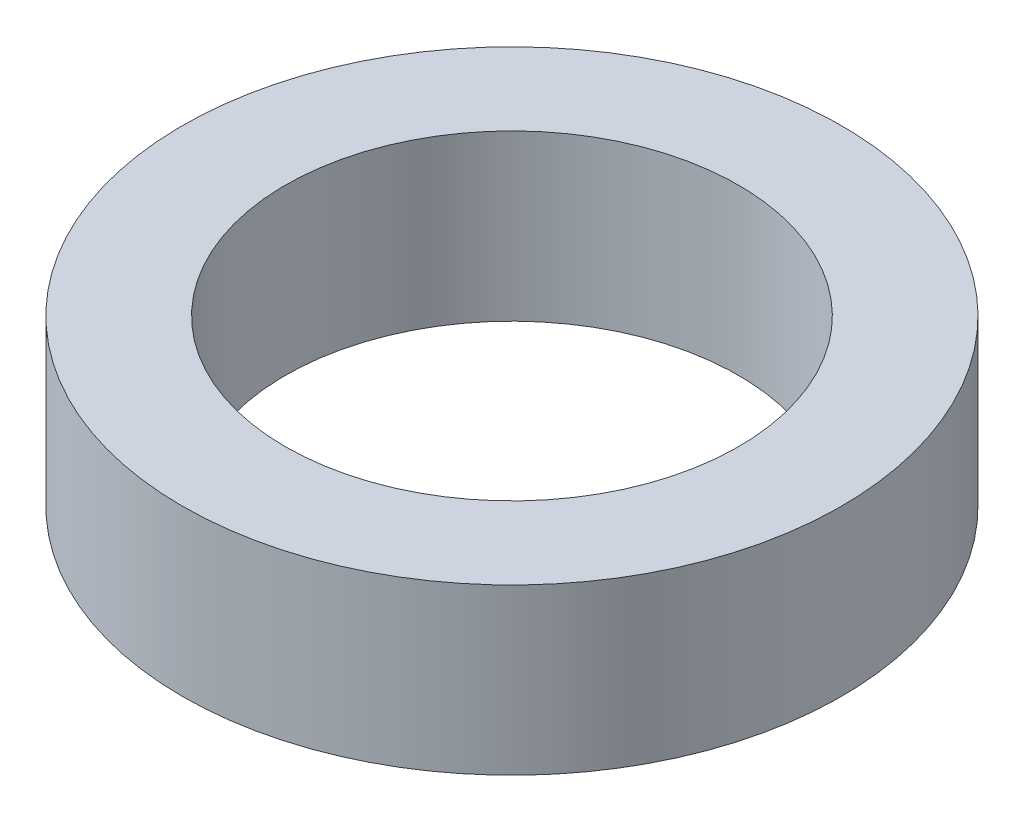
SolidWorks part; units mm, degrees
ref_plane "Front Plane" through (0, 0, 0) normal (0, 0, 1) x (1, 0, 0)
ref_plane "Top Plane" through (0, 0, 0) normal (0, 1, 0) x (1, 0, 0)
ref_plane "Right Plane" through (0, 0, 0) normal (1, 0, 0) x (0, 0, -1)
sketch "Sketch1" plane through (0, 0, 0) normal (0, 1, 0) x (1, 0, 0)
  circle A0 centre (0, 0) radius 2.1828
  circle A1 centre (0, 0) radius 3.175
  dimension "D1" = 6.35
  dimension "D2" = 4.3656
extrude "Boss-Extrude1" add sketch "Sketch1" along normal blind 1.5875
